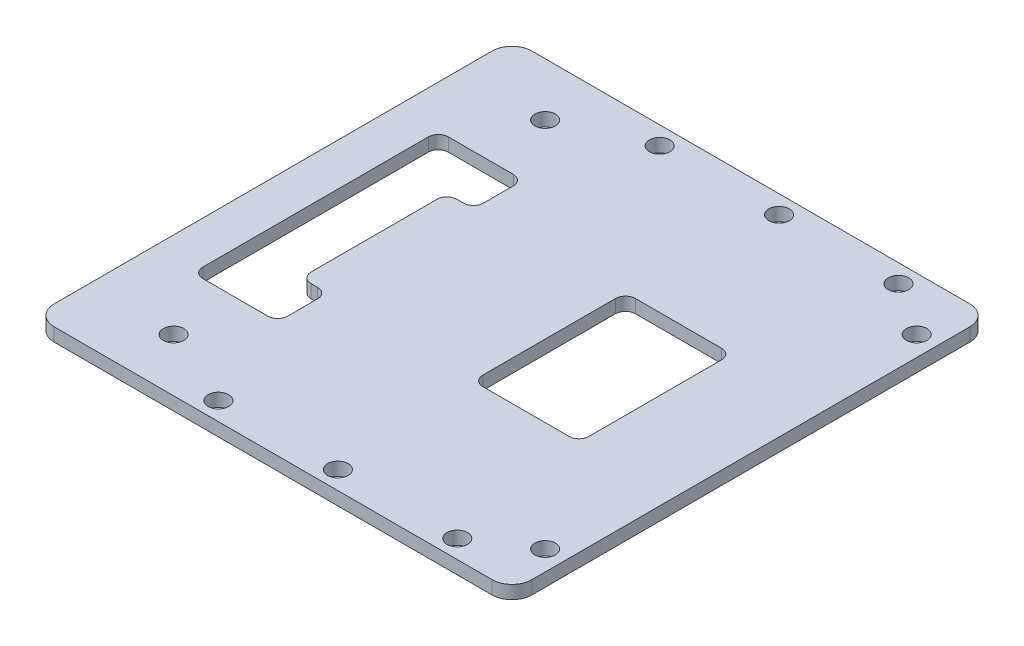
SolidWorks part; units mm, degrees
material "Thornel Mat VMA"
ref_plane "Front Plane" through (0, 0, 0) normal (0, 0, 1) x (1, 0, 0)
ref_plane "Top Plane" through (0, 0, 0) normal (0, 1, 0) x (1, 0, 0)
ref_plane "Right Plane" through (0, 0, 0) normal (1, 0, 0) x (0, 0, -1)
sketch "Sketch1" plane through (0, 0, 0) normal (0, 1, 0) x (1, 0, 0)
  line L0 (-41.9766, -33.25) -> (30.0234, -33.25) construction
  line L1 (-41.9766, -36) -> (30.0234, -36)
  line L3 (-41.9766, 36) -> (30.0234, 36)
  line L4 (30.0234, -36) -> (30.0234, 36)
  line L5 (-35.5766, -18.5) -> (-22.7766, 18.5) construction
  line L6 (-22.7766, -18.5) -> (-35.5766, 18.5) construction
  line L12 (15.6234, 11.5) -> (-0.3766, 11.5)
  line L13 (-22.7766, -18.5) -> (-27, -18.5)
  line L14 (-22.7766, -18.5) -> (-22.7766, 18.5)
  line L15 (-22.7766, 18.5) -> (-31.9766, 18.5)
  line L17 (15.6234, 11.5) -> (15.6234, -11.5)
  line L18 (15.6234, -11.5) -> (-0.3766, -11.5)
  line L19 (-49.3451, 0) -> (49.3451, 0) construction
  line L21 (-41.9766, -36) -> (-41.9766, 36)
  line L26 (-31.9766, 18.5) -> (-35.5766, 18.5)
  line L28 (-27, -18.5) -> (-35.5766, -18.5)
  line L29 (-35.5766, 18.5) -> (-35.5766, -18.5)
  line L34 (-0.3766, 11.5) -> (-0.3766, -11.5)
  line L35 (15.6234, 11.5) -> (-0.3766, -11.5) construction
  line L36 (15.6234, -11.5) -> (-0.3766, 11.5) construction
  circle A4 centre (-16.9766, -33.25) radius 1.55
  circle A5 centre (1.0234, -33.25) radius 1.55
  circle A6 centre (19.0234, -33.25) radius 1.55
  circle A7 centre (-16.9766, 33.25) radius 1.55
  circle A8 centre (1.0234, 33.25) radius 1.55
  circle A9 centre (19.0234, 33.25) radius 1.55
  circle A11 centre (-28.9766, -28) radius 1.55
  circle A12 centre (-28.9766, 28) radius 1.55
  circle A13 centre (27.0234, -28) radius 1.55
  circle A14 centre (27.0234, 28) radius 1.55
  point P0 (0, 0)
  point P6 (7.6234, 0)
  point P13 (-29.1766, 0)
  point P38 (0, 0)
  point P54 (-41.9766, 0)
  dimension "D8" = 3
  dimension "D10" = 3.1
  dimension "D2" = 72
  dimension "D3" = 16
  dimension "D4" = 23
  dimension "D5" = 56
  dimension "D6" = 37
  dimension "D7" = 22.4
  dimension "D9" = 18.6
  dimension "D11" = 18
  dimension "D12" = 18
  dimension "D13" = 2.75
  dimension "D14" = 25
  dimension "D18" = 72
  dimension "D19" = 56
extrude "Boss-Extrude1" add sketch "Sketch1" along normal blind 2
fillet "Fillet1" radius 1.5 8 edges at (-22.7766, 1, 18.5) (-22.7766, 1, -18.5) (-35.5766, 1, -18.5) (-35.5766, 1, 18.5) (-0.3766, 1, -11.5) (15.6234, 1, -11.5) (15.6234, 1, 11.5) (-0.3766, 1, 11.5)
sketch "Sketch2" plane through (0, 2, 0) normal (0, 1, 0) x (1, 0, 0)
  line L0 (-22.7766, -17) -> (-22.7766, 17) construction
  line L1 (-22.7766, -11) -> (-26.7766, -11)
  line L2 (-22.7766, -11) -> (-22.7766, 11)
  line L3 (-22.7766, 11) -> (-26.7766, 11)
  line L4 (-26.7766, -11) -> (-26.7766, 11)
  line L5 (-22.7766, -11) -> (-26.7766, 11) construction
  line L6 (-22.7766, 11) -> (-26.7766, -11) construction
  point P0 (-24.7766, 0)
  dimension "D1" = 22
  dimension "D2" = 4
extrude "Boss-Extrude2" add sketch "Sketch2" against normal up to surface (2 mm away) up to face at (27.0234, 0, -26.45)
fillet "Fillet3" radius 1.5 4 edges at (-22.7766, 1, -11) (-22.7766, 1, 11) (-26.7766, 1, 11) (-26.7766, 1, -11)
fillet "Fillet5" radius 3 4 edges at (-41.9766, 1, 36) (30.0234, 1, 36) (30.0234, 1, -36) (-41.9766, 1, -36)
